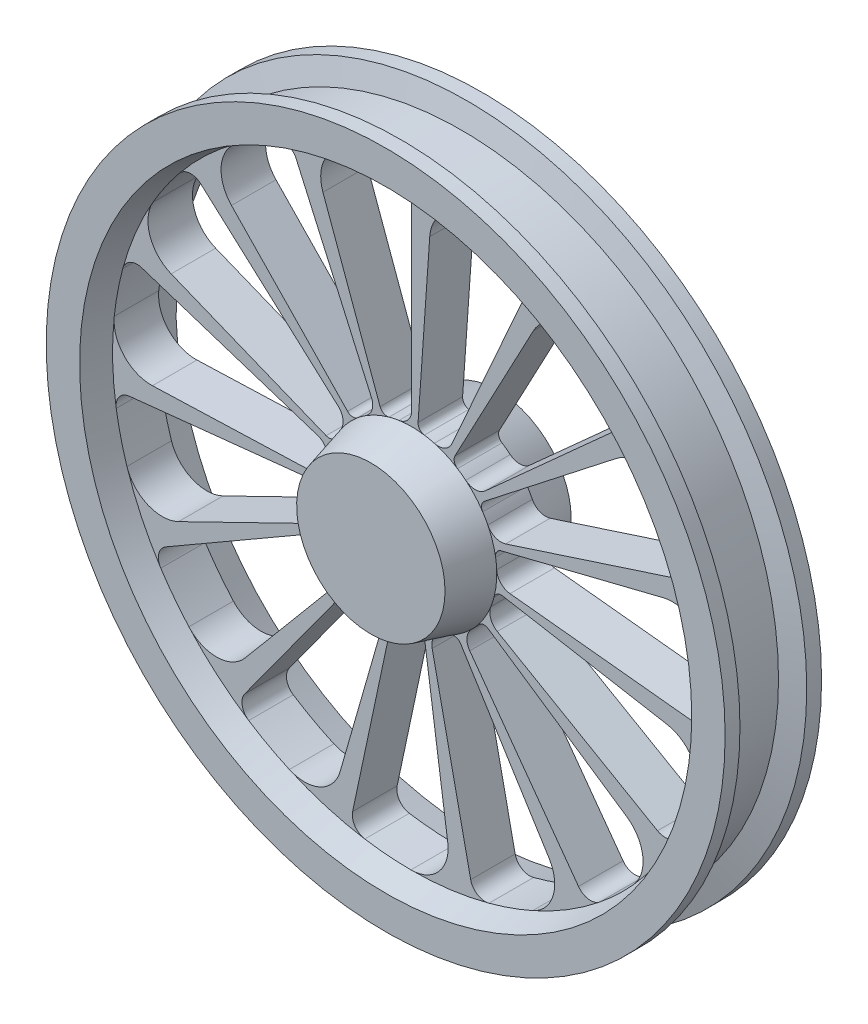
SolidWorks part; units mm, degrees
material "1060 Alloy"
ref_plane "Front Plane" through (0, 0, 0) normal (0, 0, 1) x (1, 0, 0)
ref_plane "Top Plane" through (0, 0, 0) normal (0, 1, 0) x (1, 0, 0)
ref_plane "Right Plane" through (0, 0, 0) normal (1, 0, 0) x (0, 0, -1)
sketch "Sketch1" plane through (0, 0, 0) normal (1, 0, 0) x (0, 0, -1)
  line L0 (0, 0) -> (170, 0)
  line L1 (170, 0) -> (170, 100)
  line L2 (170, 100) -> (115, 114.7372)
  line L3 (115, 114.7372) -> (115, 403.1218)
  line L4 (115, 403.1218) -> (150, 412.5)
  line L5 (150, 412.5) -> (150, 457.5)
  line L6 (150, 457.5) -> (130, 457.5)
  line L7 (130, 457.5) -> (121.9615, 427.5)
  line L8 (121.9615, 427.5) -> (48.0385, 427.5)
  line L9 (48.0385, 427.5) -> (40, 457.5)
  line L10 (40, 457.5) -> (20, 457.5)
  line L11 (20, 457.5) -> (20, 412.5)
  line L12 (20, 412.5) -> (55, 403.1218)
  line L13 (55, 403.1218) -> (55, 114.7372)
  line L14 (55, 114.7372) -> (0, 100)
  line L15 (0, 100) -> (0, 0)
  line L16 (85, 0) -> (85, 488.9047) construction
  line L17 (20, 457.5) -> (150, 457.5) construction
  line L18 (0, 100) -> (170, 100) construction
  line L19 (40, 457.5) -> (40, 407.141) construction
  line L20 (20, 412.5) -> (150, 412.5) construction
  dimension "D1" = 170
  dimension "D2" = 457.5
  dimension "D3" = 60
  dimension "D4" = 45
  dimension "D5" = 100
  dimension "D6" = 130
  dimension "D7" = 30
  dimension "D8" = 20
  dimension "D9" = 15
  dimension "D10" = 15
  dimension "D11" = 15
revolve "Revolve2" add sketch "Sketch1" angle 360 about L0
sketch "Sketch3" plane through (0, 0, -115) normal (0, 0, -1) x (-1, 0, 0)
  line L0 (-457.5, 0) -> (457.5, 0) construction
  line L1 (0, 457.5) -> (0, -457.5) construction
  line L2 (0, 457.5) -> (0, 427.5) construction
  line L3 (0, 382.5994) -> (0, 133.2446)
  line L4 (119.5579, 328.4827) -> (42.5253, 116.8374)
  line L5 (155.6172, 349.5219) -> (54.1954, 121.725)
  line L6 (284.3268, 256.009) -> (99.02, 89.158)
  line L7 (363.8736, 118.2297) -> (126.7231, 41.1748)
  line L8 (380.5035, -39.9925) -> (132.5146, -13.9278)
  line L9 (331.3408, -191.2997) -> (115.3932, -66.6223)
  line L10 (224.8863, -309.5294) -> (78.3192, -107.7971)
  line L11 (79.5469, -374.2387) -> (27.7031, -130.3329)
  line L12 (-79.5469, -374.2387) -> (-27.7031, -130.3329)
  line L13 (-224.8863, -309.5294) -> (-78.3192, -107.7971)
  line L14 (-331.3408, -191.2997) -> (-115.3932, -66.6223)
  line L15 (-380.5035, -39.9925) -> (-132.5146, -13.9278)
  line L16 (-363.8736, 118.2297) -> (-126.7231, 41.1748)
  line L17 (-284.3268, 256.009) -> (-99.02, 89.158)
  line L18 (-155.6172, 349.5219) -> (-54.1954, 121.725)
  line L19 (0, 0) -> (164.4346, 451.7805) construction
  line L20 (242.8276, 251.4553) -> (86.3708, 89.4396)
  line L21 (324.1101, 130.949) -> (115.2821, 46.577)
  line L22 (349.3511, -12.1996) -> (124.26, -4.3393)
  line L23 (314.186, -153.2388) -> (111.7522, -54.5052)
  line L24 (224.6954, -267.7816) -> (79.9215, -95.2467)
  line L25 (96.3529, -336.0225) -> (34.2716, -119.5192)
  line L26 (-48.6499, -346.1621) -> (-17.3042, -123.1257)
  line L27 (-185.2407, -296.4471) -> (-65.8879, -105.4427)
  line L28 (-289.8017, -195.4737) -> (-103.079, -69.5277)
  line L29 (-344.2533, -60.7012) -> (-122.4468, -21.5907)
  line L30 (-339.1805, 84.5672) -> (-120.6424, 30.0795)
  line L31 (-275.4602, 215.2131) -> (-97.9779, 76.5487)
  line L32 (-164.1104, 308.6467) -> (-58.3721, 109.7819)
  line L33 (-24.3844, 348.7125) -> (-8.6732, 124.0328)
  circle A0 centre (0, 0) radius 457.5 construction
  circle A1 centre (0, 0) radius 403.1218 construction
  circle A2 centre (0, 0) radius 114.7372 construction
  circle A3 centre (0, 0) radius 403.1218
  circle A4 centre (0, 0) radius 114.7372
  arc A5 (0, 133.2446) -> (17.0313, 113.4661) centre (20, 133.2446) ccw
  arc A6 (0, 382.5994) -> (21.0441, 402.5721) centre (20, 382.5994) cw
  arc A7 (42.5253, 116.8374) -> (30.4725, 110.6167) centre (33.1284, 120.2576) cw
  arc A8 (119.5579, 328.4827) -> (82.8493, 394.5164) centre (72.5733, 345.5837) ccw
  arc A9 (155.6172, 349.5219) -> (182.9655, 359.2085) centre (173.8881, 341.3872) cw
  arc A10 (54.1954, 121.725) -> (61.7097, 96.7292) centre (72.4664, 113.5902) ccw
  arc A11 (284.3268, 256.009) -> (313.2506, 253.7345) centre (297.7094, 241.1461) cw
  arc A12 (99.02, 89.158) -> (95.7179, 63.267) centre (112.4026, 74.2951) ccw
  arc A13 (363.8736, 118.2297) -> (389.3718, 104.3875) centre (370.054, 99.2086) cw
  arc A14 (126.7231, 41.1748) -> (113.1757, 18.8653) centre (132.9035, 22.1537) ccw
  arc A15 (380.5035, -39.9925) -> (398.1671, -63.009) centre (378.4129, -59.883) cw
  arc A16 (132.5146, -13.9278) -> (111.0643, -28.7984) centre (130.4241, -33.8183) ccw
  arc A17 (331.3408, -191.2997) -> (338.1157, -219.5107) centre (321.3408, -208.6202) cw
  arc A18 (115.3932, -66.6223) -> (89.7489, -71.4826) centre (105.3932, -83.9428) ccw
  arc A19 (224.8863, -309.5294) -> (219.601, -338.0571) centre (208.7059, -321.2851) cw
  arc A20 (78.3192, -107.7971) -> (52.9151, -101.8067) centre (62.1389, -119.5528) ccw
  arc A21 (79.5469, -374.2387) -> (63.1153, -398.1503) centre (59.9839, -378.3969) cw
  arc A22 (27.7031, -130.3329) -> (6.9319, -114.5276) centre (8.1402, -134.4911) ccw
  arc A23 (-79.5469, -374.2387) -> (-104.2836, -389.3997) centre (-99.1098, -370.0804) cw
  arc A24 (-27.7031, -130.3329) -> (-40.25, -107.4456) centre (-47.2661, -126.1746) ccw
  arc A25 (-224.8863, -309.5294) -> (-253.651, -313.3183) centre (-241.0666, -297.7737) cw
  arc A26 (-78.3192, -107.7971) -> (-80.4723, -81.7853) centre (-94.4995, -96.0414) ccw
  arc A27 (-331.3408, -191.2997) -> (-359.1597, -183.0614) centre (-341.3408, -173.9792) cw
  arc A28 (-115.3932, -66.6223) -> (-106.7802, -41.9836) centre (-125.3932, -49.3018) ccw
  arc A29 (-380.5035, -39.9925) -> (-402.5665, -21.1515) centre (-382.594, -20.1021) cw
  arc A30 (-132.5146, -13.9278) -> (-114.6248, 5.0775) centre (-134.6052, 5.9626) ccw
  arc A31 (-363.8736, 118.2297) -> (-376.3659, 144.4157) centre (-357.6933, 137.2508) cw
  arc A32 (-126.7231, 41.1748) -> (-102.6498, 51.2607) centre (-120.5428, 60.196) ccw
  arc A33 (-284.3268, 256.009) -> (-285.0882, 285.0121) centre (-270.9441, 270.8719) cw
  arc A34 (-99.02, 89.158) -> (-72.9256, 88.5804) centre (-85.6374, 104.0209) ccw
  arc A35 (-155.6172, 349.5219) -> (-144.5161, 376.3273) centre (-137.3463, 357.6567) cw
  arc A36 (-54.1954, 121.725) -> (-30.592, 110.5837) centre (-35.9245, 129.8597) ccw
  arc A37 (242.8276, 251.4553) -> (236.1508, 326.7108) centre (206.8606, 286.1882) ccw
  arc A38 (86.3708, 89.4396) -> (72.8299, 88.6591) centre (79.1774, 96.3862) cw
  arc A39 (324.1101, 130.949) -> (348.6198, 202.414) centre (305.3798, 177.3082) ccw
  arc A40 (115.2821, 46.577) -> (102.5943, 51.3715) centre (111.536, 55.8488) cw
  arc A41 (349.3511, -12.1996) -> (400.8092, 43.1179) centre (351.096, 37.7699) ccw
  arc A42 (124.26, -4.3393) -> (114.6193, 5.2013) centre (124.609, 5.6547) cw
  arc A43 (314.186, -153.2388) -> (383.6951, -123.6336) centre (336.1046, -108.2991) ccw
  arc A44 (111.7522, -54.5052) -> (106.8255, -41.8682) centre (116.1359, -45.5173) cw
  arc A45 (224.6954, -267.7816) -> (300.2366, -269.0077) centre (262.9976, -235.6422) ccw
  arc A46 (79.9215, -95.2467) -> (80.5606, -81.6983) centre (87.5819, -88.8188) cw
  arc A47 (96.3529, -336.0225) -> (164.8644, -367.868) centre (144.416, -322.2406) ccw
  arc A48 (34.2716, -119.5192) -> (40.3661, -107.4021) centre (43.8842, -116.7628) cw
  arc A49 (-48.6499, -346.1621) -> (0.9858, -403.1206) centre (0.8635, -353.1207) ccw
  arc A50 (-17.3042, -123.1257) -> (-6.8081, -114.535) centre (-7.4015, -124.5174) cw
  arc A51 (-185.2407, -296.4471) -> (-163.0634, -368.6699) centre (-142.8383, -322.943) ccw
  arc A52 (-65.8879, -105.4427) -> (-52.8051, -101.8638) centre (-57.4074, -110.7419) cw
  arc A53 (-289.8017, -195.4737) -> (-298.9174, -270.4729) centre (-261.842, -236.9256) ccw
  arc A54 (-103.079, -69.5277) -> (-89.6717, -71.5795) centre (-97.4871, -77.818) cw
  arc A55 (-344.2533, -60.7012) -> (-383.0858, -125.5086) centre (-335.5709, -109.9415) ccw
  arc A56 (-122.4468, -21.5907) -> (-111.0331, -28.9183) centre (-120.7103, -31.4387) cw
  arc A57 (-339.1805, 84.5672) -> (-401.0153, 41.1572) centre (-351.2766, 36.0524) ccw
  arc A58 (-120.6424, 30.0795) -> (-113.196, 18.743) centre (-123.0616, 20.3766) cw
  arc A59 (-275.4602, 215.2131) -> (-349.6055, 200.7066) centre (-306.2433, 175.8126) ccw
  arc A60 (-97.9779, 76.5487) -> (-95.7862, 63.1635) centre (-104.1345, 68.6686) cw
  arc A61 (-164.1104, 308.6467) -> (-237.7458, 325.552) centre (-208.2577, 285.1731) ccw
  arc A62 (-58.3721, 109.7819) -> (-61.8141, 96.6625) centre (-67.2016, 105.0872) cw
  arc A63 (-24.3844, 348.7125) -> (-84.7777, 394.1065) centre (-74.2626, 345.2247) ccw
  arc A64 (-8.6732, 124.0328) -> (-17.1538, 113.4477) centre (-18.6489, 123.3353) cw
  point P29 (0, 0)
  point P30 (0, 0)
  point P113 (0, 0)
  point P199 (0, 0)
  circle M2 centre (0, 0) radius 403.1218
  circle M3 centre (0, 0) radius 114.7372
  dimension "D1" = 20
  dimension "D2" = 20
  dimension "D3" = 10
  dimension "D4" = 50
  dimension "D5" = 20
  dimension "D6" = 15
  dimension "D7" = 15
extrude "Cut-Extrude1" cut sketch "Sketch3" against normal up to next contours L4 A8 A3 A6 L3 A5 A7 M3 | A38 L20 A37 A9 L5 A10 M2 M3 | A40 L21 A39 A11 L6 A12 A4 M2 | A42 L22 A41 A13 L7 A14 M2 M3 | A44 L23 A43 A15 L8 A16 A4 M2 | A46 L24 A45 A17 L9 A18 M2 M3 | A48 L25 A47 A19 L10 A20 A4 M2 | A50 L26 A49 A21 L11 A22 M2 M3 | A52 L27 A51 A23 L12 A24 A4 M2 | A54 L28 A53 A25 L13 A26 M2 M3 | A56 L29 A55 A27 L14 A28 A4 M2 | A58 L30 A57 A29 L15 A30 M2 M3 | A60 L31 A59 A31 L16 A32 A4 M2 | A62 L32 A61 A33 L17 A34 M2 M3 | A64 L33 A63 A3 A35 L18 A36 A4
equation "\"A\"= 130"
equation "\"B\"= 915"
equation "\"D2@Sketch1\"=\"B\"/2"
equation "\"D6@Sketch1\"=\"A\""
